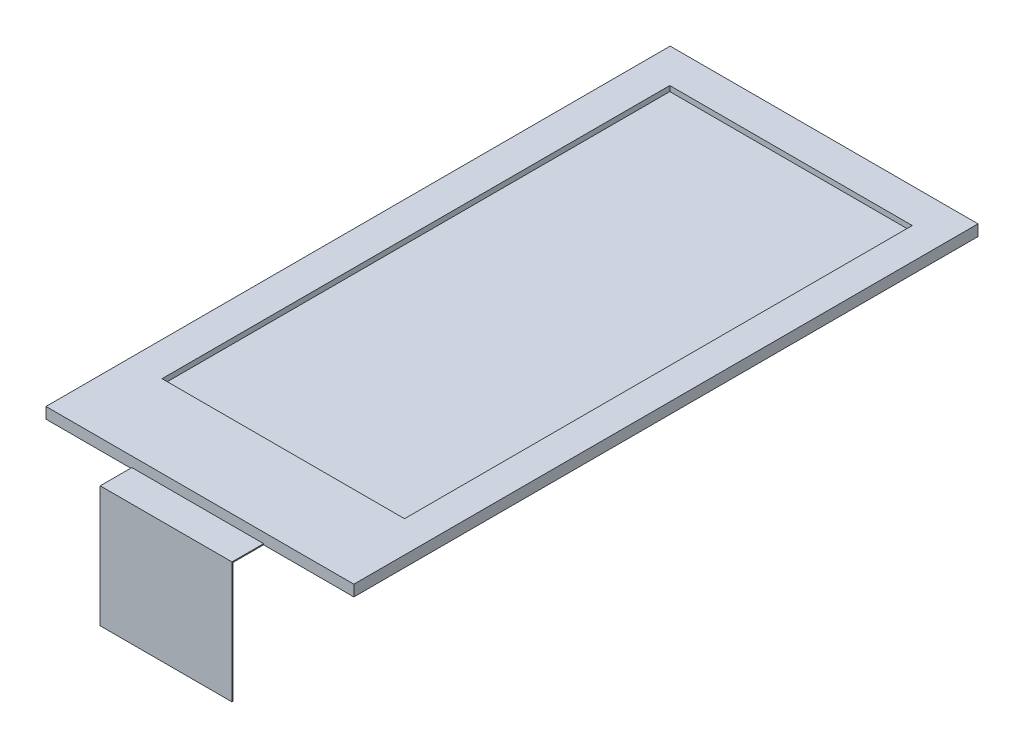
SolidWorks part; units mm, degrees
ref_plane "Front Plane" through (0, 0, 0) normal (0, 0, 1) x (1, 0, 0)
ref_plane "Top Plane" through (0, 0, 0) normal (0, 1, 0) x (1, 0, 0)
ref_plane "Right Plane" through (0, 0, 0) normal (1, 0, 0) x (0, 0, -1)
sketch "Sketch1" plane through (0, 0, 0) normal (0, 1, 0) x (1, 0, 0)
  line L1 (3.25, 0) -> (26.95, 0)
  line L2 (0, -3.25) -> (0, -61.75)
  line L3 (3.25, -65) -> (26.95, -65)
  line L4 (30.2, -3.25) -> (30.2, -61.75)
  arc A0 (0, -61.75) -> (3.25, -65) centre (3.25, -61.75) ccw
  arc A1 (26.95, -65) -> (30.2, -61.75) centre (26.95, -61.75) ccw
  arc A2 (26.95, 0) -> (30.2, -3.25) centre (26.95, -3.25) cw
  arc A3 (3.25, 0) -> (0, -3.25) centre (3.25, -3.25) ccw
  point P9 (30.2, -65)
  point P12 (30.2, 0)
  point P15 (0, 0)
  dimension "D3" = 3.25
  dimension "D1" = 30.2
  dimension "D2" = 65
extrude "Boss-Extrude1" add sketch "Sketch1" along normal blind 1.5
sketch "Sketch2" plane through (0, 1.5, 0) normal (0, 1, 0) x (1, 0, 0)
  line L0 (0, -3.25) -> (0, -61.75) construction
  line L1 (0.5, -2.9) -> (29.7, -2.9)
  line L2 (0.5, -2.9) -> (0.5, -62.1)
  line L3 (0.5, -62.1) -> (29.7, -62.1)
  line L4 (29.7, -2.9) -> (29.7, -62.1)
  line L5 (26.95, 0) -> (3.25, 0) construction
  point P4 (0.5, -32.5)
  point P7 (0, -32.5)
  point P10 (15.1, -2.9)
  point P11 (15.1, 0)
  dimension "D1" = 29.2
  dimension "D2" = 59.2
extrude "Boss-Extrude2" add sketch "Sketch2" along normal blind 1.05
sketch "Sketch3" plane through (0, 1.5, 0) normal (0, 1, 0) x (1, 0, 0)
  line L0 (0.5, -62.1) -> (29.7, -62.1) construction
  line L1 (21.14, -62.1) -> (8.64, -62.1)
  line L2 (21.14, -62.1) -> (21.14, -76.4)
  line L3 (21.14, -76.4) -> (8.64, -76.4)
  line L4 (8.64, -62.1) -> (8.64, -76.4)
  dimension "D1" = 12.5
  dimension "D2" = 14.3
  dimension "D3" = 8.56
extrude "Boss-Extrude3" add sketch "Sketch3" along normal blind 0.1
sketch "Sketch4" plane through (0, 1.6, 0) normal (0, 1, 0) x (1, 0, 0)
  line L0 (21.14, -76.4) -> (21.14, -62.1) construction
  line L1 (8.64, -76.4) -> (21.14, -76.4)
  line L2 (8.64, -76.4) -> (8.64, -72.9)
  line L3 (8.64, -72.9) -> (21.14, -72.9)
  line L4 (21.14, -76.4) -> (21.14, -72.9)
  dimension "D1" = 3.5
extrude "Boss-Extrude4" add sketch "Sketch4" along normal blind 0.2
sketch "Sketch5" plane through (0, 0, 65) normal (0, 0, 1) x (1, 0, 0)
  line L0 (29.7, 2.55) -> (29.7, 1.5) construction
  line L1 (21.14, 1.5) -> (8.64, 1.5)
  line L2 (21.14, 1.5) -> (21.14, -9.9)
  line L3 (21.14, -9.9) -> (8.64, -9.9)
  line L4 (8.64, 1.5) -> (8.64, -9.9)
  line L5 (3.25, 1.5) -> (8.64, 1.5) construction
  point P7 (-36.1309, 23.664)
  dimension "D1" = 11.4
  dimension "D2" = 8.56
  dimension "D3" = 12.5
extrude "Boss-Extrude5" add sketch "Sketch5" along normal blind 0.1
sketch "Sketch6" plane through (0, 0, 76.4) normal (0, 0, 1) x (1, 0, 0)
  line L8 (8.64, 1.5) -> (21.14, 1.5)
  line L9 (21.14, 1.5) -> (21.14, 1.8)
  line L10 (21.14, 1.8) -> (8.64, 1.8)
  line L11 (8.64, 1.8) -> (8.64, 1.5)
  line L12 (8.64, 1.5) -> (21.14, 1.5)
  line L13 (21.14, 1.5) -> (21.14, 1.8)
  line L14 (21.14, 1.8) -> (8.64, 1.8)
  line L15 (8.64, 1.8) -> (8.64, 1.5)
  dimension "D1" = 0
extrude "Cut-Extrude1" cut sketch "Sketch6" against normal up to surface (11.3 mm away) up to face at (14.89, -4.2, 65.1)
sketch "Sketch7" [suppressed] plane through (0, 0, 65) normal (0, 0, -1) x (-1, 0, 0)
  line L0 (-8.64, 0) -> (-8.64, -9.9) construction
  line L1 (-21.14, -9.9) -> (-8.64, -9.9)
  line L2 (-21.14, -9.9) -> (-21.14, -6.4)
  line L3 (-21.14, -6.4) -> (-8.64, -6.4)
  line L4 (-8.64, -9.9) -> (-8.64, -6.4)
  dimension "D1" = 3.5
extrude "Boss-Extrude6" [suppressed] add sketch "Sketch7" along normal blind 0.2
sketch "Sketch8" plane through (0, 0, 0) normal (0, -1, 0) x (1, 0, 0)
  line L6 (0, 61.75) -> (0, 3.25)
  line L7 (3.25, 0) -> (26.95, 0)
  line L8 (30.2, 3.25) -> (30.2, 61.75)
  line L9 (26.95, 65) -> (21.14, 65)
  line L10 (21.14, 65) -> (8.64, 65)
  line L11 (21.14, 65) -> (8.64, 65)
  line L12 (0, 61.75) -> (0, 3.25)
  line L13 (3.25, 0) -> (26.95, 0)
  line L14 (30.2, 3.25) -> (30.2, 61.75)
  line L15 (26.95, 65) -> (21.14, 65)
  line L16 (8.64, 65) -> (3.25, 65)
  line L17 (8.64, 65) -> (3.25, 65)
  arc A4 (3.25, 65) -> (0, 61.75) centre (3.25, 61.75) ccw
  arc A5 (0, 3.25) -> (3.25, 0) centre (3.25, 3.25) ccw
  arc A6 (26.95, 0) -> (30.2, 3.25) centre (26.95, 3.25) ccw
  arc A7 (30.2, 61.75) -> (26.95, 65) centre (26.95, 61.75) ccw
  arc A8 (3.25, 65) -> (0, 61.75) centre (3.25, 61.75) ccw
  arc A9 (0, 3.25) -> (3.25, 0) centre (3.25, 3.25) ccw
  arc A10 (26.95, 0) -> (30.2, 3.25) centre (26.95, 3.25) ccw
  arc A11 (30.2, 61.75) -> (26.95, 65) centre (26.95, 61.75) ccw
  dimension "D1" = 0
extrude "Cut-Extrude2" cut sketch "Sketch8" against normal up to surface (1.5 mm away) up to face at (15.0475, 1.5, 40.2625)
sketch "Sketch10" plane through (0, 2.55, 0) normal (0, 1, 0) x (1, 0, 0)
  line L1 (3.7217, -54.3176) -> (26.7226, -54.3176)
  line L2 (3.7217, -54.3176) -> (3.7217, -6.1557)
  line L3 (3.7217, -6.1557) -> (26.7226, -6.1557)
  line L4 (26.7226, -54.3176) -> (26.7226, -6.1557)
extrude "Cut-Extrude3" cut sketch "Sketch10" against normal blind 0.5
